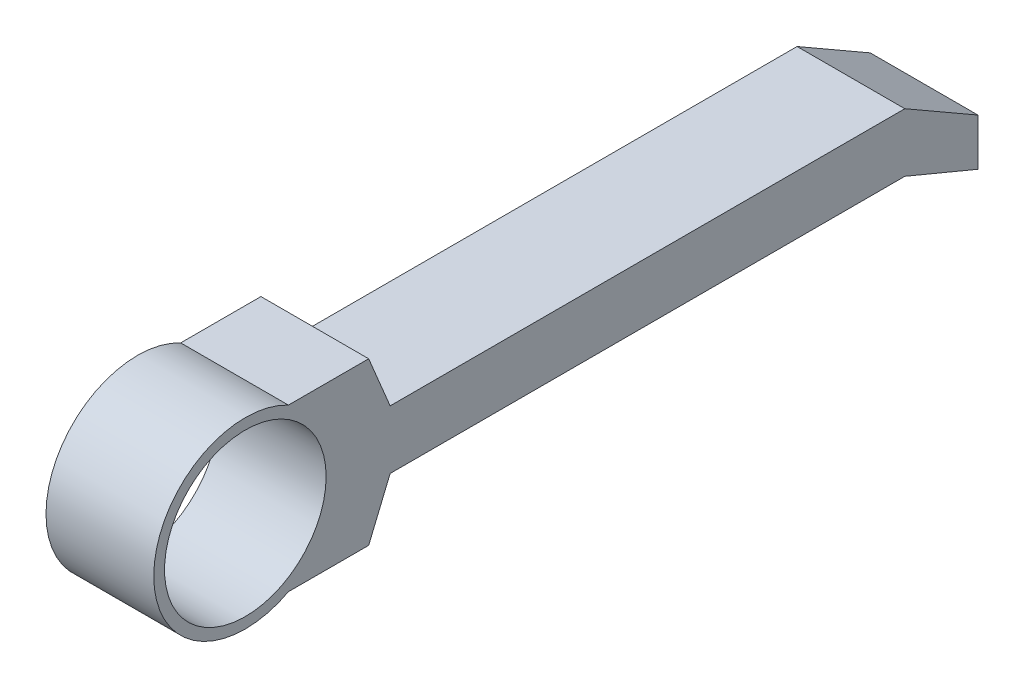
SolidWorks part; units mm, degrees
ref_plane "Alzado" through (0, 0, 0) normal (0, 0, 1) x (1, 0, 0)
ref_plane "Planta" through (0, 0, 0) normal (0, 1, 0) x (1, 0, 0)
ref_plane "Vista lateral" through (0, 0, 0) normal (1, 0, 0) x (0, 0, -1)
sketch "Croquis2" plane through (0, 0, 0) normal (1, 0, 0) x (0, 0, -1)
  line L0 (0, 0) -> (13.6, 0) construction
  line L1 (0.8, -1.5) -> (2.2896, -1.5)
  line L2 (2.2896, -1.5) -> (2.688, -0.5436)
  line L3 (2.688, -0.5436) -> (12.2417, -0.5436)
  line L4 (12.2417, -0.5436) -> (13.6, -1.1094)
  line L5 (12.2417, 0.5436) -> (13.6, -0.2379)
  line L6 (2.688, 0.5436) -> (12.2417, 0.5436)
  line L7 (2.2896, 1.5) -> (2.688, 0.5436)
  line L8 (0, 1.5) -> (2.2896, 1.5)
  line L9 (13.6, -0.2379) -> (13.6, -1.1094)
  circle A0 centre (0, 0) radius 1.5
  circle A1 centre (0, 0) radius 1.7
  dimension "D2" = 3
  dimension "D3" = 3.4
  dimension "D1" = 13.6
extrude "Saliente-Extruir1" add sketch "Croquis2" along normal blind 2
